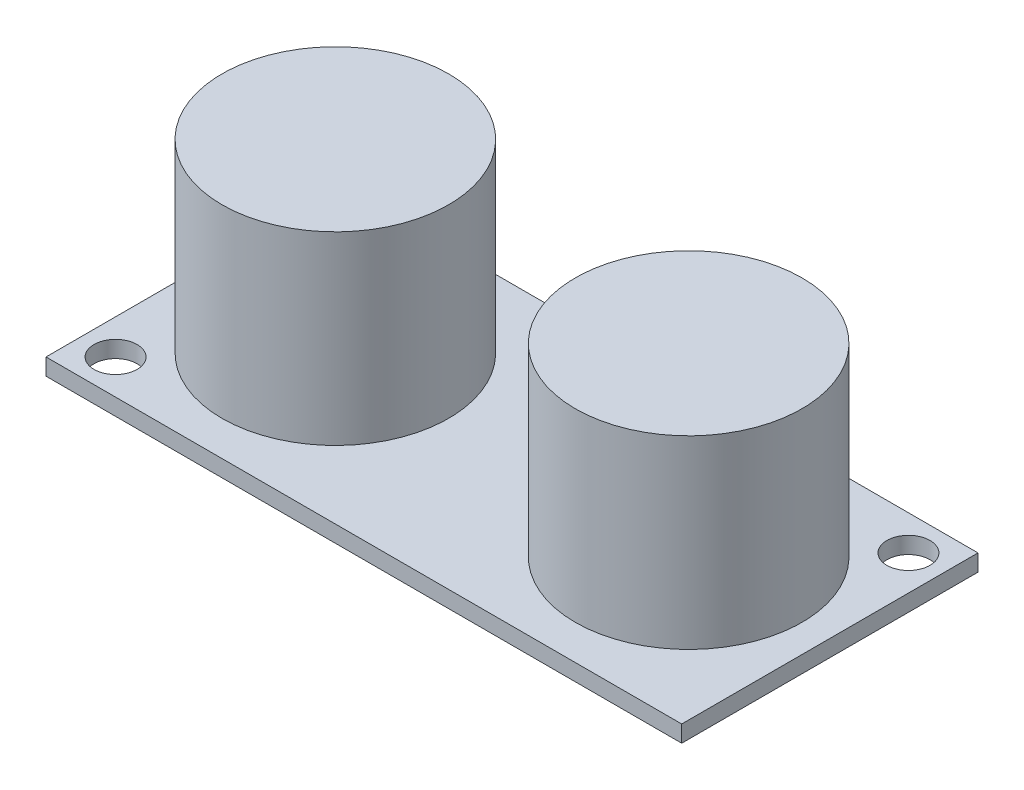
SolidWorks part; units mm, degrees
ref_plane "Front Plane" through (0, 0, 0) normal (0, 0, 1) x (1, 0, 0)
ref_plane "Top Plane" through (0, 0, 0) normal (0, 1, 0) x (1, 0, 0)
ref_plane "Right Plane" through (0, 0, 0) normal (1, 0, 0) x (0, 0, -1)
sketch "Sketch1" plane through (0, 0, 0) normal (0, 1, 0) x (1, 0, 0)
  line L0 (-22.85, 0) -> (22.85, 0) construction
  line L1 (-22.85, -10.65) -> (22.85, -10.65)
  line L2 (-22.85, -10.65) -> (-22.85, 10.65)
  line L3 (-22.85, 10.65) -> (22.85, 10.65)
  line L4 (22.85, -10.65) -> (22.85, 10.65)
  line L5 (-22.85, -10.65) -> (22.85, 10.65) construction
  line L6 (-22.85, 10.65) -> (22.85, -10.65) construction
  line L7 (-20.35, -8.15) -> (20.35, -8.15) construction
  line L8 (-20.35, -8.15) -> (-20.35, 8.15) construction
  line L9 (-20.35, 8.15) -> (20.35, 8.15) construction
  line L10 (20.35, -8.15) -> (20.35, 8.15) construction
  line L11 (-20.35, -8.15) -> (20.35, 8.15) construction
  line L12 (-20.35, 8.15) -> (20.35, -8.15) construction
  circle A0 centre (20.35, 8.15) radius 1.55
  circle A1 centre (-20.35, -8.15) radius 1.55
  point P0 (0, 0)
  point P6 (0, 0)
  dimension "D5" = 3.1
  dimension "D1" = 45.7
  dimension "D2" = 21.3
  dimension "D3" = 2.5
  dimension "D4" = 2.5
extrude "Boss-Extrude1" add sketch "Sketch1" along normal blind 1.2
sketch "Sketch2" plane through (0, 1.2, 0) normal (0, 1, 0) x (1, 0, 0)
  line L0 (-12.7, 0) -> (12.7, 0) construction
  circle A0 centre (-12.7, 0) radius 8.15
  circle A1 centre (12.7, 0) radius 8.15
  dimension "D3" = 16.3
  dimension "D1" = 25.4
extrude "Boss-Extrude2" add sketch "Sketch2" along normal blind 13.3
